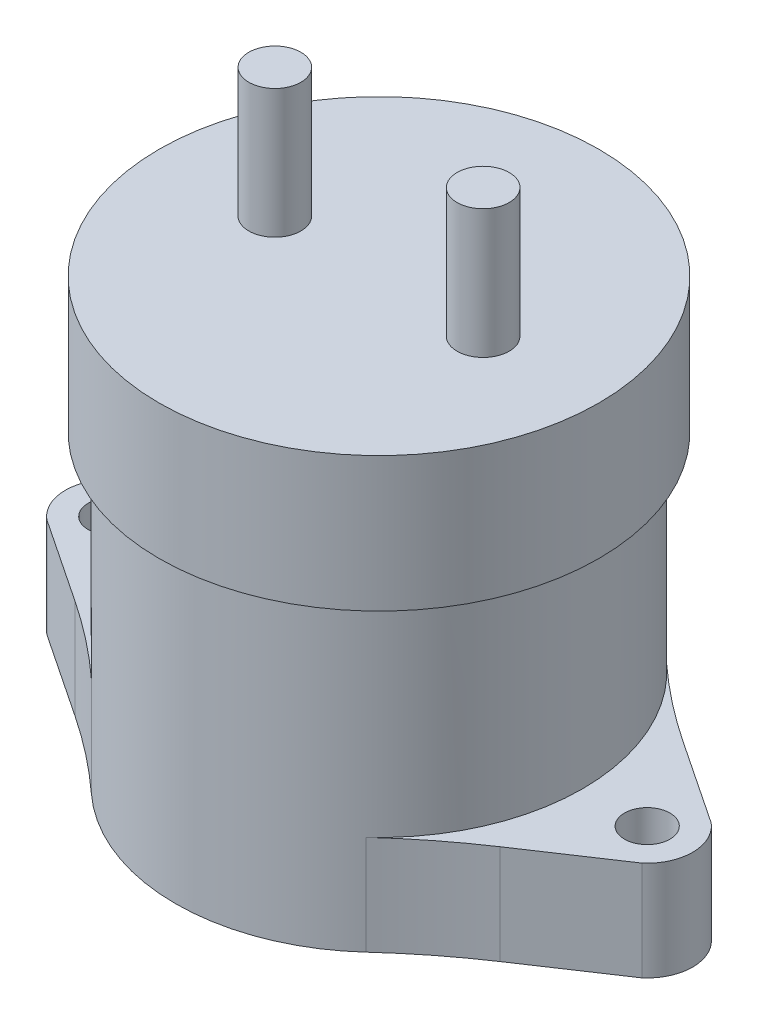
SolidWorks part; units mm, degrees
ref_plane "Front Plane" through (0, 0, 0) normal (0, 0, 1) x (1, 0, 0)
ref_plane "Top Plane" through (0, 0, 0) normal (0, 1, 0) x (1, 0, 0)
ref_plane "Right Plane" through (0, 0, 0) normal (1, 0, 0) x (0, 0, -1)
sketch "Sketch1" plane through (0, 0, 0) normal (0, 1, 0) x (1, 0, 0)
  circle A0 centre (0, 0) radius 26
extrude "Boss-Extrude1" add sketch "Sketch1" along normal blind 14.2
sketch "Sketch4" plane through (0, 0, 0) normal (0, -1, 0) x (1, 0, 0)
  line L1 (0, 26) -> (0, -26) construction
  line L2 (27.1291, -11.6796) -> (37.9901, -4.433)
  line L3 (27.1291, 11.6796) -> (37.9901, 4.433)
  line L4 (-27.1291, 11.6796) -> (-37.9901, 4.433)
  line L5 (-27.1291, -11.6796) -> (-37.9901, -4.433)
  circle A0 centre (0, 0) radius 26 construction
  arc A11 (-17.5451, -19.1878) -> (17.5451, -19.1878) centre (0, 0) ccw
  arc A15 (17.5451, 19.1878) -> (-17.5451, 19.1878) centre (0, 0) ccw
  circle A20 centre (34.25, 0) radius 2.9
  arc A21 (37.9901, -4.433) -> (37.9901, 4.433) centre (34.25, 0) ccw
  arc A22 (17.5451, -19.1878) -> (27.1291, -11.6796) centre (71.53, -78.227) cw
  arc A23 (17.5451, 19.1878) -> (27.1291, 11.6796) centre (71.53, 78.227) ccw
  arc A24 (-37.9901, -4.433) -> (-37.9901, 4.433) centre (-34.25, 0) cw
  circle A25 centre (34.25, 0) radius 5.8 construction
  circle A26 centre (-34.25, 0) radius 2.9
  arc A27 (-17.5451, 19.1878) -> (-27.1291, 11.6796) centre (-71.53, 78.227) cw
  arc A28 (-17.5451, -19.1878) -> (-27.1291, -11.6796) centre (-71.53, -78.227) ccw
  point P21 (40.05, 0)
extrude "Boss-Extrude2" add sketch "Sketch4" against normal blind 12.7
sketch "Sketch8" plane through (0, 14.2, 0) normal (0, 1, 0) x (1, 0, 0)
  circle A0 centre (0, 0) radius 26
extrude "Boss-Extrude3" add sketch "Sketch8" along normal blind 25
sketch "Sketch9" plane through (0, 39.2, 0) normal (0, 1, 0) x (1, 0, 0)
  circle A0 centre (0, 0) radius 28.075
extrude "Boss-Extrude4" add sketch "Sketch9" along normal blind 17.2
sketch "Sketch10" plane through (0, 56.4, 0) normal (0, 1, 0) x (1, 0, 0)
  circle A0 centre (13.3, 0) radius 3.325
  circle A1 centre (-13.3, 0) radius 3.325
extrude "Boss-Extrude5" add sketch "Sketch10" along normal blind 16.45
